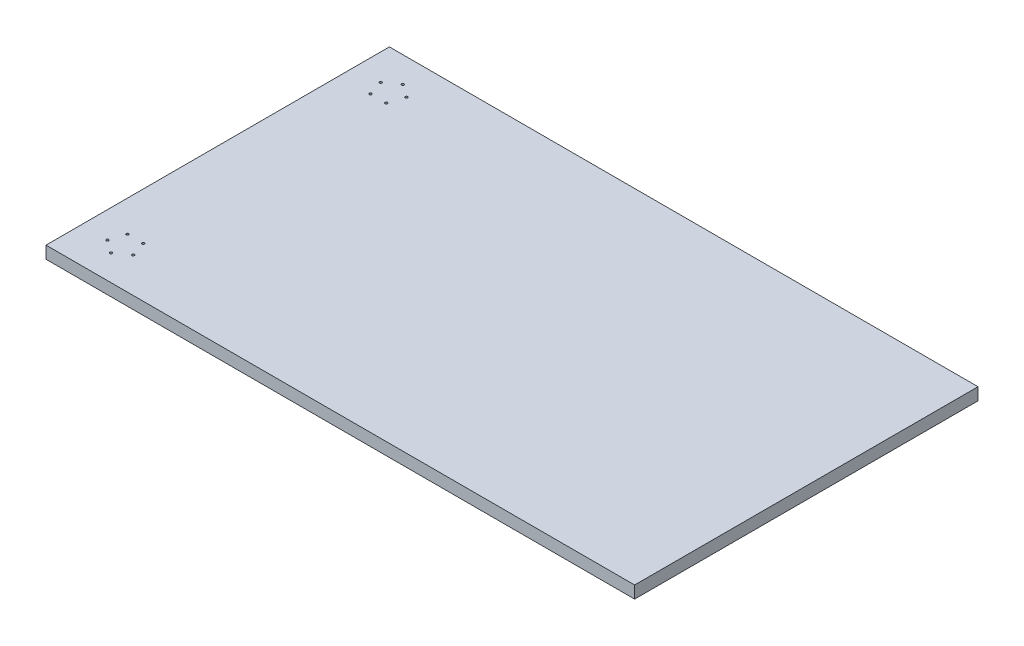
SolidWorks part; units mm, degrees
ref_plane "Front Plane" through (0, 0, 0) normal (0, 0, 1) x (1, 0, 0)
ref_plane "Top Plane" through (0, 0, 0) normal (0, 1, 0) x (1, 0, 0)
ref_plane "Right Plane" through (0, 0, 0) normal (1, 0, 0) x (0, 0, -1)
sketch "Sketch1" plane through (0, 0, 0) normal (0, 1, 0) x (1, 0, 0)
  line L1 (-600, -350) -> (600, -350)
  line L2 (-600, -350) -> (-600, 350)
  line L3 (-600, 350) -> (600, 350)
  line L4 (600, -350) -> (600, 350)
  line L5 (-600, -350) -> (600, 350) construction
  line L6 (-600, 350) -> (600, -350) construction
  point P0 (0, 0)
  dimension "D1" = 1200
  dimension "D2" = 700
extrude "Boss-Extrude1" add sketch "Sketch1" along normal blind 25 contours L2 L1 L4 L3
sketch "Sketch2" plane through (0, 25, 0) normal (0, 1, 0) x (1, 0, 0)
  line L0 (-6.2005, 0) -> (-205.2788, 0) construction
  line L1 (-600, -350) -> (-600, 350) construction
  line L2 (-600, 350) -> (600, 350) construction
  circle A0 centre (-520, 270) radius 27.5 construction
  circle A1 centre (-520, 297.5) radius 3
  circle A2 centre (-493.8459, 278.498) radius 3
  circle A3 centre (-503.8359, 247.752) radius 3
  circle A4 centre (-536.1641, 247.752) radius 3
  circle A5 centre (-546.1541, 278.498) radius 3
  circle A6 centre (-520, -270) radius 27.5 construction
  circle A7 centre (-546.1541, -278.498) radius 3
  circle A8 centre (-536.1641, -247.752) radius 3
  circle A9 centre (-503.8359, -247.752) radius 3
  circle A10 centre (-493.8459, -278.498) radius 3
  circle A11 centre (-520, -297.5) radius 3
  point P22 (-520, 270)
  dimension "D1" = 55
  dimension "D2" = 80
  dimension "D3" = 80
  dimension "D4" = 6
  dimension "D5" = 5
hole_wizard "Tap Drill for M6 Tap1" positions "3DSketch1" profile "Sketch3" hole size "M6" standard "ISO"
sketch3d "3DSketch1"
  point P0 (-493.8459, 25, -278.498)
  point P3 (-520, 25, -297.5)
  point P6 (-546.1541, 25, -278.498)
  point P9 (-536.1641, 25, -247.752)
  point P12 (-503.8359, 25, -247.752)
  point P15 (-493.8459, 25, 278.498)
  point P18 (-503.8359, 25, 247.752)
  point P21 (-536.1641, 25, 247.752)
  point P24 (-546.1541, 25, 278.498)
  point P27 (-520, 25, 297.5)
sketch "Sketch3" plane through (-493.8459, 25, -278.498) normal (1, 0, 0) x (0, 0, 1)
  line L0 (0, 0) -> (0, 16.5022)
  line L1 (0, 16.5022) -> (2.5, 15)
  line L2 (2.5, 15) -> (2.5, 0)
  line L5 (2.5, 0) -> (0, 0)
  line L10 (0, 16.5022) -> (-2.5, 15) construction
  line L11 (0, -6.35) -> (0, 107.95) construction
  dimension "Hole Dia." = 5
  dimension "Hole Depth" = 15
  dimension "Drill Angle" = 118
